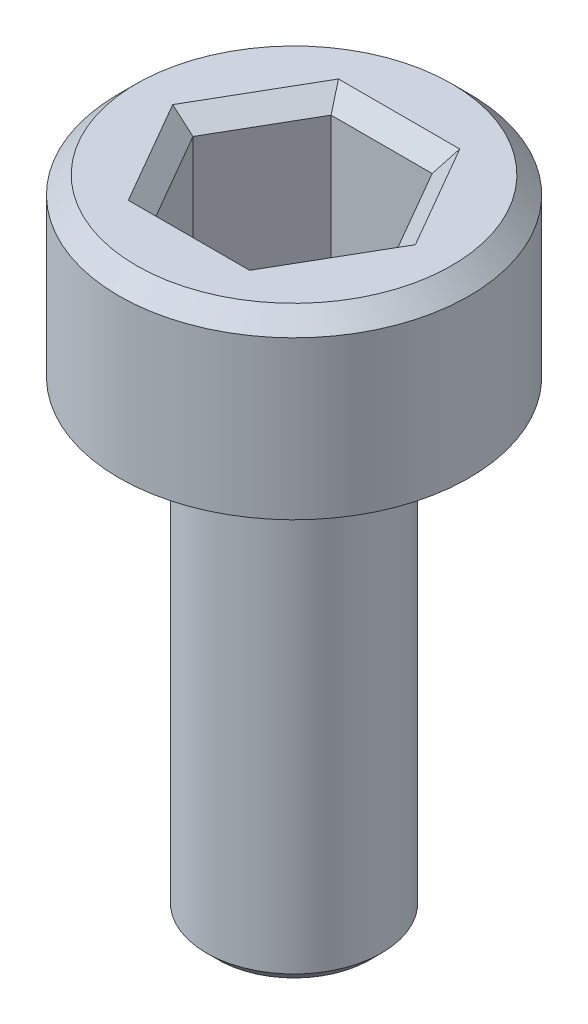
SolidWorks part; units mm, degrees
ref_plane "Front Plane" through (0, 0, 0) normal (0, 0, 1) x (1, 0, 0)
ref_plane "Top Plane" through (0, 0, 0) normal (0, 1, 0) x (1, 0, 0)
ref_plane "Right Plane" through (0, 0, 0) normal (1, 0, 0) x (0, 0, -1)
sketch "Sketch1" plane through (0, 0, 0) normal (0, 1, 0) x (1, 0, 0)
  circle A0 centre (0, 0) radius 3
  dimension "D1" = 6
extrude "Boss-Extrude1" add sketch "Sketch1" along normal blind 3
chamfer "Chamfer1" distance 0.3 angle 45 1 edges at (0, 3, 3)
sketch "Sketch2" plane through (0, 3, 0) normal (0, 1, 0) x (1, 0, 0)
  line L1 (1.7321, 0) -> (0.866, 1.5)
  line L2 (0.866, 1.5) -> (-0.866, 1.5)
  line L3 (-0.866, 1.5) -> (-1.7321, 0)
  line L4 (-1.7321, 0) -> (-0.866, -1.5)
  line L5 (-0.866, -1.5) -> (0.866, -1.5)
  line L6 (0.866, -1.5) -> (1.7321, 0)
  circle A0 centre (0, 0) radius 1.5 construction
  dimension "D1" = 3
extrude "Cut-Extrude1" cut sketch "Sketch2" against normal blind 2.5
chamfer "Chamfer2" distance 0.3 angle 45 6 edges at (1.299, 3, -0.75) (1.299, 3, 0.75) (0, 3, 1.5) (-1.299, 3, 0.75) (-1.299, 3, -0.75) (0, 3, -1.5)
sketch "Sketch3" plane through (0, 0, 0) normal (0, -1, 0) x (1, 0, 0)
  circle A0 centre (0, 0) radius 1.5
  dimension "D1" = 3
extrude "Boss-Extrude2" add sketch "Sketch3" along normal blind 8
chamfer "Chamfer3" distance 0.2 angle 45 1 edges at (0, -8, -1.5)
